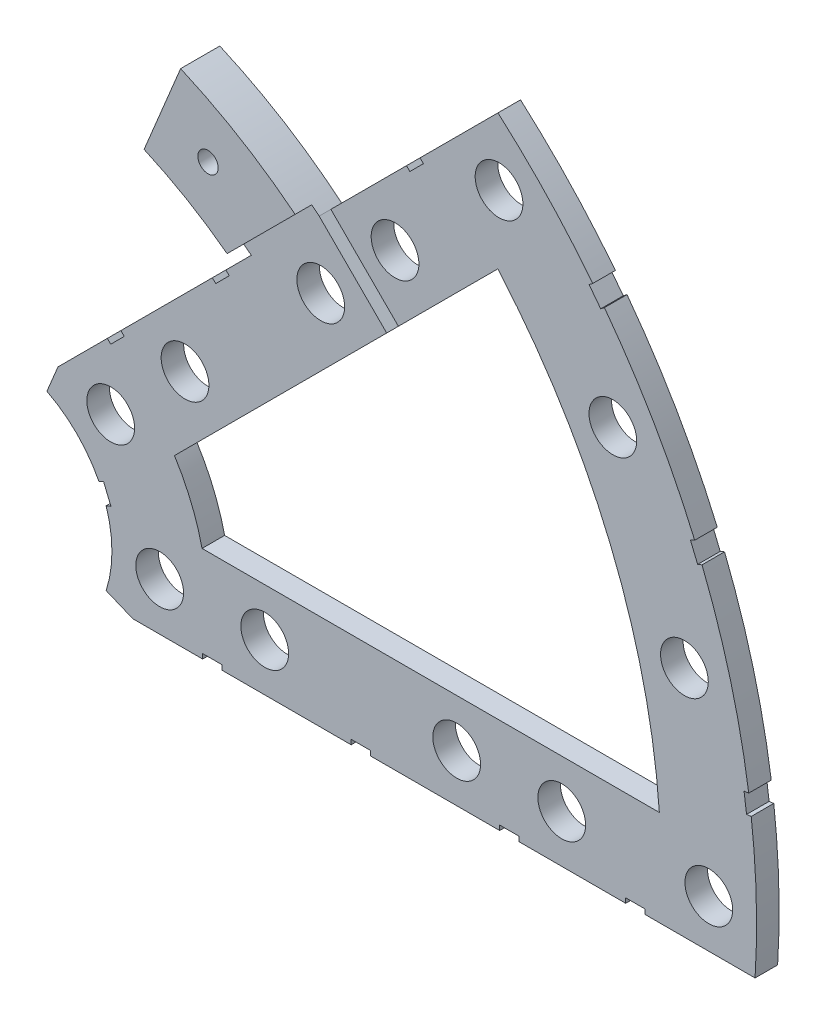
SolidWorks part; units mm, degrees
material "Brass"
ref_plane "Front Plane" through (0, 0, 0) normal (0, 0, 1) x (1, 0, 0)
ref_plane "Top Plane" through (0, 0, 0) normal (0, 1, 0) x (1, 0, 0)
ref_plane "Right Plane" through (0, 0, 0) normal (1, 0, 0) x (0, 0, -1)
sketch "Sketch1" plane through (0, 0, 0) normal (0, 0, 1) x (1, 0, 0)
  line L0 (0, 0) -> (320.3893, 0) construction
  line L1 (0, 0) -> (155.5285, 155.5285) construction
  line L2 (27.2188, 62.3934) -> (22.3577, 50.6576)
  line L3 (8.6967, 17.6769) -> (7.229, 14.1336)
  line L4 (101.4014, -6.35) -> (18.6489, -6.35)
  line L5 (15.1056, -4.8823) -> (18.6489, -6.35)
  line L6 (88.6729, 6.35) -> (27.8605, 6.35)
  line L7 (67.2115, 76.1917) -> (43.4342, 52.4144)
  line L8 (34.4055, 43.3857) -> (8.6967, 17.6769)
  line L9 (67.1914, 58.2111) -> (24.1905, 15.2102)
  line L10 (0, 0) -> (40.4486, 97.6516) construction
  line L11 (0, 0) -> (123.4567, -51.1374) construction
  line L18 (8.6967, 17.6769) -> (13.294, 8.6183) construction
  line L19 (18.6489, -6.35) -> (15.4943, 3.3063) construction
  line L20 (27.8605, 6.35) -> (27.7442, 6.7059) construction
  line L21 (24.1905, 15.2102) -> (24.3599, 14.8764) construction
  line L22 (67.2115, 76.1917) -> (8.6967, 17.6769) construction
  arc A0 (7.229, 14.1336) -> (15.1056, -4.8823) centre (0, 0) cw
  arc A1 (67.2115, 76.1917) -> (101.4014, -6.35) centre (0, 0) cw
  arc A2 (24.1905, 15.2102) -> (27.8605, 6.35) centre (0, 0) cw
  arc A3 (67.1914, 58.2111) -> (88.6729, 6.35) centre (0, 0) cw
  arc A4 (27.2188, 62.3934) -> (43.4342, 52.4144) centre (0, 0) cw
  arc A5 (22.3577, 50.6576) -> (34.4055, 43.3857) centre (0, 0) cw
  arc A8 (13.294, 8.6183) -> (15.4943, 3.3063) centre (0, 0) cw construction
  arc A9 (24.3599, 14.8764) -> (27.7442, 6.7059) centre (0, 0) cw construction
  dimension "D1" = 45
  dimension "D3" = 6.35
  dimension "D4" = 15.875
  dimension "D7" = 22.5
  dimension "D8" = 101.6
  dimension "D11" = 12.7
  dimension "D12" = 12.7
  dimension "D2" = 55.372
  dimension "D13" = 12.7
  dimension "D5" = 67.5
  dimension "D9" = 1.27
  dimension "D10" = 1.27
  dimension "D14" = 6.35
  dimension "D15" = 6.35
  dimension "D16" = 1.27
  dimension "D6" = 12.7
extrude "Boss-Extrude1" add sketch "Sketch1" along normal blind 3
sketch "Sketch2" plane through (0, 0, 3) normal (0, 0, 1) x (1, 0, 0)
  line L0 (0, 0) -> (101.6, 0) construction
  line L1 (0, 0) -> (71.842, 71.842) construction
  line L3 (0, 0) -> (22.225, 0) construction
  line L4 (0, 0) -> (15.7154, 15.7154) construction
  line L5 (0, 0) -> (95.25, 0) construction
  line L6 (0, 0) -> (92.0044, 24.6525) construction
  arc A0 (101.4014, -6.35) -> (67.2115, 76.1917) centre (0, 0) ccw construction
  circle A1 centre (22.225, 0) radius 3.175
  arc A2 (15.1056, -4.8823) -> (7.229, 14.1336) centre (0, 0) ccw construction
  circle A3 centre (36.195, 0) radius 3.175
  circle A4 centre (61.722, 0) radius 3.175
  circle A5 centre (75.692, 0) radius 3.175
  circle A6 centre (95.25, 0) radius 3.175
  circle A7 centre (15.7154, 15.7154) radius 3.175
  circle A8 centre (25.5937, 25.5937) radius 3.175
  circle A9 centre (43.644, 43.644) radius 3.175
  circle A10 centre (53.5223, 53.5223) radius 3.175
  circle A11 centre (92.0044, 24.6525) radius 3.175
  circle A12 centre (82.4889, 47.625) radius 3.175
  circle A13 centre (67.3519, 67.3519) radius 3.175
  dimension "D3" = 6.35
  dimension "D1" = 45
  dimension "D2" = 6.35
  dimension "D4" = 6.35
  dimension "D5" = 13.97
  dimension "D7" = 13.97
  dimension "D8" = 19.558
  dimension "D9" = 45
  dimension "D10" = 15
  dimension "D11" = 25.527
  dimension "D6" = 2
extrude "Cut-Extrude1" cut sketch "Sketch2" against normal through all
sketch "Sketch3" plane through (0, 0, 3) normal (0, 0, 1) x (1, 0, 0)
  line L0 (15.2664, 24.2467) -> (17.0625, 26.0427)
  line L1 (15.2664, 24.2467) -> (15.7154, 23.7977)
  line L2 (17.0625, 26.0427) -> (17.5115, 25.5937)
  line L3 (15.7154, 23.7977) -> (17.5115, 25.5937)
  line L5 (43.4342, 52.4144) -> (44.9911, 53.9713)
  line L6 (43.4342, 52.4144) -> (52.4144, 43.4342)
  line L7 (44.9911, 53.9713) -> (53.9713, 44.9911)
  line L8 (52.4144, 43.4342) -> (53.9713, 44.9911)
  line L9 (27.94, -6.35) -> (30.48, -6.35)
  line L10 (27.94, -6.35) -> (27.94, -5.715)
  line L11 (30.48, -6.35) -> (30.48, -5.715)
  line L12 (27.94, -5.715) -> (30.48, -5.715)
  line L13 (18.6489, -6.35) -> (101.4014, -6.35) construction
  line L14 (67.437, -6.35) -> (69.977, -6.35)
  line L15 (67.437, -6.35) -> (67.437, -5.715)
  line L16 (69.977, -6.35) -> (69.977, -5.715)
  line L17 (67.437, -5.715) -> (69.977, -5.715)
  line L18 (29.2307, 38.211) -> (31.0268, 40.007)
  line L19 (29.2307, 38.211) -> (29.6797, 37.762)
  line L20 (31.0268, 40.007) -> (31.4758, 39.558)
  line L21 (29.6797, 37.762) -> (31.4758, 39.558)
  line L22 (56.845, 65.8253) -> (55.049, 64.0292)
  line L23 (56.845, 65.8253) -> (57.294, 65.3763)
  line L24 (55.049, 64.0292) -> (55.498, 63.5802)
  line L25 (57.294, 65.3763) -> (55.498, 63.5802)
  line L26 (47.6885, -6.35) -> (50.2285, -6.35)
  line L27 (47.6885, -6.35) -> (47.6885, -5.715)
  line L28 (50.2285, -6.35) -> (50.2285, -5.715)
  line L29 (47.6885, -5.715) -> (50.2285, -5.715)
  line L30 (84.201, -6.35) -> (86.741, -6.35)
  line L31 (84.201, -6.35) -> (84.201, -5.715)
  line L32 (86.741, -6.35) -> (86.741, -5.715)
  line L33 (84.201, -5.715) -> (86.741, -5.715)
  line L34 (0, 0) -> (100.7308, 13.2615) construction
  line L35 (0, 0) -> (93.8662, 38.8806) construction
  line L36 (0, 0) -> (80.6047, 61.8502) construction
  line L37 (0, 0) -> (101.6, 0) construction
  line L38 (99.9355, 14.4377) -> (100.267, 11.9194)
  line L39 (99.9355, 14.4377) -> (101.1946, 14.6035)
  line L40 (100.267, 11.9194) -> (101.5261, 12.0852)
  line L41 (101.1946, 14.6035) -> (101.5261, 12.0852)
  line L42 (99.9355, 14.4377) -> (101.5261, 12.0852) construction
  line L43 (100.267, 11.9194) -> (101.1946, 14.6035) construction
  line L44 (93.7655, 37.4643) -> (94.9388, 37.9503)
  line L45 (93.7655, 37.4643) -> (92.7935, 39.811)
  line L46 (94.9388, 37.9503) -> (93.9668, 40.297)
  line L47 (92.7935, 39.811) -> (93.9668, 40.297)
  line L48 (93.7655, 37.4643) -> (93.9668, 40.297) construction
  line L49 (94.9388, 37.9503) -> (92.7935, 39.811) construction
  line L50 (79.3278, 62.4712) -> (80.874, 60.456)
  line L51 (79.3278, 62.4712) -> (80.3354, 63.2443)
  line L52 (80.874, 60.456) -> (81.8816, 61.2292)
  line L53 (80.3354, 63.2443) -> (81.8816, 61.2292)
  line L54 (79.3278, 62.4712) -> (81.8816, 61.2292) construction
  line L55 (80.874, 60.456) -> (80.3354, 63.2443) construction
  line L56 (13.5939, 7.0054) -> (14.5659, 4.6588)
  line L57 (13.5939, 7.0054) -> (14.7672, 7.4914)
  line L58 (14.5659, 4.6588) -> (15.7393, 5.1448)
  line L59 (14.7672, 7.4914) -> (15.7393, 5.1448)
  line L60 (13.5939, 7.0054) -> (15.7393, 5.1448) construction
  line L61 (14.5659, 4.6588) -> (14.7672, 7.4914) construction
  line L62 (34.4055, 43.3857) -> (8.6967, 17.6769) construction
  line L63 (67.2115, 76.1917) -> (43.4342, 52.4144) construction
  circle A0 centre (15.7154, 15.7154) radius 3.175 construction
  circle A1 centre (53.5223, 53.5223) radius 3.175 construction
  circle A2 centre (22.225, 0) radius 3.175 construction
  circle A3 centre (61.722, 0) radius 3.175 construction
  arc A4 (101.4014, -6.35) -> (67.2115, 76.1917) centre (0, 0) ccw construction
  arc A9 (15.1056, -4.8823) -> (7.229, 14.1336) centre (0, 0) ccw construction
  circle A10 centre (25.5937, 25.5937) radius 3.175 construction
  circle A11 centre (36.195, 0) radius 3.175 construction
  circle A12 centre (75.692, 0) radius 3.175 construction
  circle A13 centre (53.5223, 53.5223) radius 3.175 construction
  point P75 (14.6666, 6.0751)
  dimension "D2" = 5.715
  dimension "D3" = 2.54
  dimension "D8" = 0.635
  dimension "D9" = 5.715
  dimension "D12" = 5.715
  dimension "D4" = 7.5
  dimension "D5" = 22.5
  dimension "D7" = 37.5
  dimension "D10" = 90
  dimension "D11" = 1.27
  dimension "D14" = 0.635
  dimension "D15" = 90
  dimension "D18" = 0.635
  dimension "D19" = 90
  dimension "D22" = 0.635
  dimension "D20" = 1.27
  dimension "D17" = 0.635
  dimension "D6" = 12.7
  dimension "D21" = 5.715
  dimension "D13" = 11.4935
  dimension "D16" = 11.4935
  dimension "D23" = 8.509
  dimension "D24" = 8.509
extrude "Cut-Extrude2" cut sketch "Sketch3" against normal through all
sketch "Sketch4" plane through (0, 0, 3) normal (0, 0, 1) x (1, 0, 0)
  line L0 (22.3577, 50.6576) -> (27.2188, 62.3934)
  line L1 (42.4435, 53.2198) -> (33.3932, 44.1696)
  line L2 (55.049, 64.0292) -> (44.9911, 53.9713) construction
  arc A0 (43.4342, 52.4144) -> (27.2188, 62.3934) centre (0, 0) ccw construction
  arc A1 (34.4055, 43.3857) -> (22.3577, 50.6576) centre (0, 0) ccw construction
  arc A2 (33.3932, 44.1696) -> (22.3577, 50.6576) centre (0, 0) ccw
  arc A3 (42.4435, 53.2198) -> (27.2188, 62.3934) centre (0, 0) ccw
  dimension "D2" = 55.372
  dimension "D3" = 68.072
  dimension "D1" = 1.27
extrude "Boss-Extrude2" add sketch "Sketch4" along normal blind 2.207
hole_wizard "#6-32 Tapped Hole1" positions "Sketch6" profile "Sketch5" tap size "#6-32" standard "ANSI Inch" end condition through all
sketch "Sketch6" plane through (0, 0, 0) normal (0, 0, -1) x (-1, 0, 0)
  line L0 (0, 0) -> (-67.3519, 67.3519) construction
  line L2 (0, 0) -> (-30.861, 53.4528) construction
  arc A0 (-27.2188, 62.3934) -> (-43.4342, 52.4144) centre (0, 0) ccw construction
  point P0 (-30.861, 53.4528)
  dimension "D1" = 15
  dimension "D2" = 6.35
cosmetic thread "Hole Thread1" parameters "D2"=3.5052
sketch "Sketch5" plane through (30.861, 53.4528, 0) normal (1, 0, 0) x (0, 1, 0)
  line L0 (0, 0) -> (0, 5.207)
  line L1 (0, 5.207) -> (1.3525, 5.207)
  line L2 (1.3525, 5.207) -> (1.3525, 0)
  line L5 (1.3525, 0) -> (0, 0)
  line L11 (0, -6.35) -> (0, 107.95) construction
  dimension "Thru Tap Drill Dia." = 2.7051
  dimension "Thru Tap Drill Depth" = 5.207
equation "\"LayerThick\"= 3mm"
equation "\"D1@Boss-Extrude1\"=\"LayerThick\""
equation "\"D1@Boss-Extrude2\"=.205-\"LayerThick\""
equation "\"CoilSep\"= 1.005"
equation "\"D11@Sketch2\"=\"CoilSep\""
equation "\"CoilSep2\"= \"D8@Sketch2\""
equation "\"D13@Sketch3\"=\"CoilSep\"/2-.05"
equation "\"D16@Sketch3\"=\"CoilSep\"/2-.05"
equation "\"D23@Sketch3\"=\"CoilSep2\"/2-.05"
equation "\"D24@Sketch3\"=\"CoilSep2\"/2-.05"
